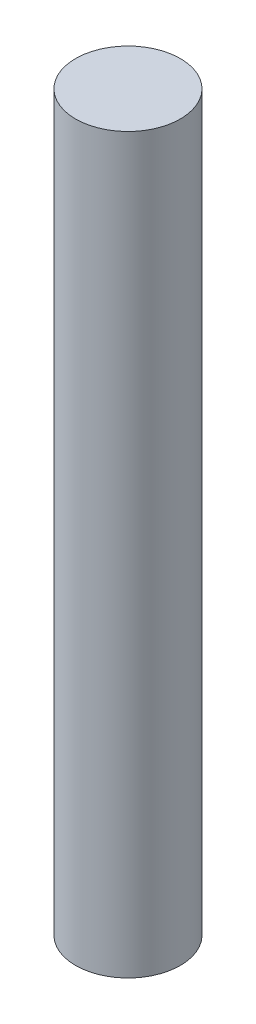
SolidWorks part; units mm, degrees
ref_plane "Front Plane" through (0, 0, 0) normal (0, 0, 1) x (1, 0, 0)
ref_plane "Top Plane" through (0, 0, 0) normal (0, 1, 0) x (1, 0, 0)
ref_plane "Right Plane" through (0, 0, 0) normal (1, 0, 0) x (0, 0, -1)
sketch "Sketch1" plane through (0, 0, 0) normal (0, 1, 0) x (1, 0, 0)
  circle A0 centre (-7.8859, -0.2979) radius 2.54
  dimension "D1" = 5.08
extrude "Boss-Extrude1" add sketch "Sketch1" along normal blind 35.56
